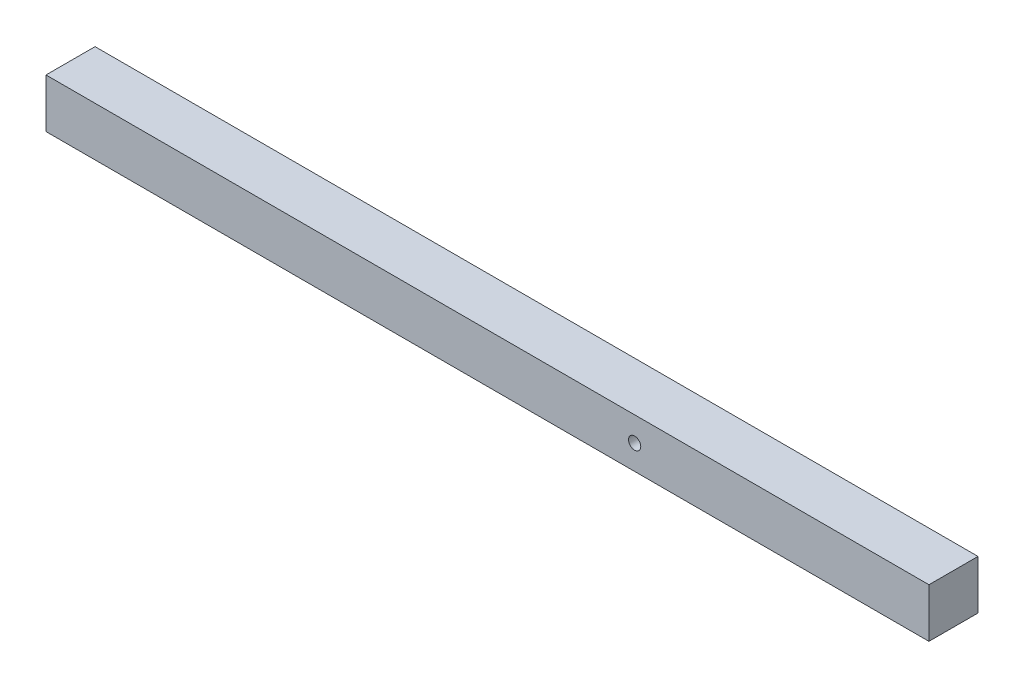
SolidWorks part; units mm, degrees
ref_plane "Front Plane" through (0, 0, 0) normal (0, 0, 1) x (1, 0, 0)
ref_plane "Top Plane" through (0, 0, 0) normal (0, 1, 0) x (1, 0, 0)
ref_plane "Right Plane" through (0, 0, 0) normal (1, 0, 0) x (0, 0, -1)
sketch "Sketch1" plane through (0, 0, 0) normal (0, 1, 0) x (1, 0, 0)
  line L1 (-457.2, -25.4) -> (457.2, -25.4)
  line L2 (-457.2, -25.4) -> (-457.2, 25.4)
  line L3 (-457.2, 25.4) -> (457.2, 25.4)
  line L4 (457.2, -25.4) -> (457.2, 25.4)
  line L5 (-457.2, -25.4) -> (457.2, 25.4) construction
  line L6 (-457.2, 25.4) -> (457.2, -25.4) construction
  point P0 (0, 0)
  dimension "D1" = 914.4
  dimension "D2" = 50.8
extrude "Boss-Extrude1" add sketch "Sketch1" along normal blind 50.8
sketch "Sketch2" plane through (0, 0, 0) normal (0, 0, 1) x (1, 0, 0)
  line L0 (457.2, 50.8) -> (457.2, 0) construction
  line L2 (-457.2, 0) -> (457.2, 0) construction
  circle A0 centre (152.4, 25.4) radius 6.35
  point P6 (170.5306, 0)
  dimension "D3" = 12.7
  dimension "D1" = 304.8
  dimension "D2" = 25.4
extrude "Cut-Extrude1" cut sketch "Sketch2" along normal through all both and the other way through all
